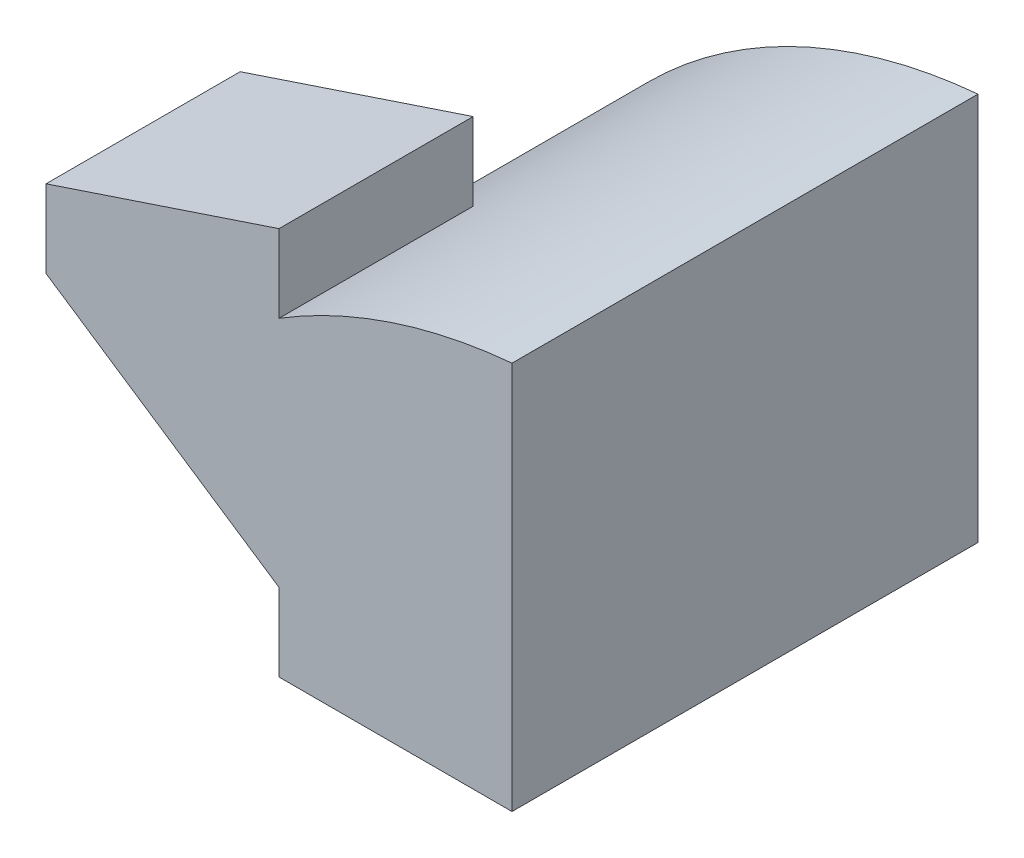
SolidWorks part; units mm, degrees
ref_plane "Front" through (0, 0, 0) normal (0, 0, 1) x (1, 0, 0)
ref_plane "Top" through (0, 0, 0) normal (0, 1, 0) x (1, 0, 0)
ref_plane "Right" through (0, 0, 0) normal (1, 0, 0) x (0, 0, -1)
sketch "Sketch1" plane through (0, 0, 0) normal (0, 1, 0) x (1, 0, 0)
  line L1 (-3, -3) -> (3, -3)
  line L2 (-3, -3) -> (-3, 3)
  line L3 (-3, 3) -> (3, 3)
  line L4 (3, -3) -> (3, 3)
  line L5 (-3, -3) -> (3, 3) construction
  line L6 (-3, 3) -> (3, -3) construction
  point P0 (0, 0)
  dimension "D1" = 6
  dimension "D2" = 6
extrude "Boss-Extrude1" add sketch "Sketch1" along normal blind 5
sketch "Sketch13" plane through (0, 0, -3) normal (0, 0, -1) x (-1, 0, 0)
  line L0 (3, 0) -> (-3, 0) construction
  line L1 (-3, 5) -> (-3, 0) construction
  line L6 (-3, 0) -> (3, 0)
  line L7 (-3, 5) -> (-3, 0)
  line L8 (3, 5) -> (-3, 5)
  line L9 (3, 0) -> (3, 5)
  line L10 (-3, 0) -> (3, 0)
  line L11 (-3, 5) -> (-3, 0)
  line L12 (3, 5) -> (-3, 5)
  line L13 (3, 0) -> (3, 5)
  arc A0 (-3, 5) -> (3, 0) centre (-3.6111, -1.8333) cw
  point P3 (0, 4)
  line M6 (3, 0) -> (3, 5)
  line M7 (3, 5) -> (-3, 5)
  dimension "D1" = 4
  dimension "D2" = 3
  dimension "D3" = 0
extrude "Cut-Extrude12" cut sketch "Sketch13" against normal blind 3.5 contours A0 M7 M6
sketch "Sketch14" plane through (0, 0, 0.5) normal (0, 0, -1) x (-1, 0, 0)
  line L0 (0, 4) -> (0, 5)
  line L2 (3, 5) -> (-3, 5)
  line L3 (3, 0) -> (3, 5)
  line L4 (3, 5) -> (-3, 5)
  line L5 (3, 0) -> (3, 5)
  arc A1 (3, 0) -> (-3, 5) centre (-3.6111, -1.8333) ccw
  arc A2 (3, 0) -> (-3, 5) centre (-3.6111, -1.8333) ccw
  line M4 (3, 5) -> (-3, 5)
  arc M5 (-3, 5) -> (3, 0) centre (-3.6111, -1.8333) cw
  dimension "D1" = 0
extrude "Cut-Extrude13" cut sketch "Sketch14" against normal blind 3.5 contours L0 M5 M4
sketch "Sketch15" plane through (0, 0, 3) normal (0, 0, 1) x (1, 0, 0)
  line L0 (0, 5) -> (-3, 4)
  line L1 (-3, 5) -> (-3, 0) construction
  line L2 (-3, 3) -> (0, 1)
  line L3 (0, 1) -> (0, 0)
  line L7 (3, 0) -> (3, 5)
  line L8 (0, 4) -> (0, 5)
  line L9 (0, 5) -> (-3, 5)
  line L10 (-3, 5) -> (-3, 0)
  line L11 (-3, 0) -> (3, 0)
  line L12 (3, 0) -> (3, 5)
  line L13 (0, 4) -> (0, 5)
  line L14 (0, 5) -> (-3, 5)
  line L15 (-3, 5) -> (-3, 0)
  line L16 (-3, 0) -> (3, 0)
  arc A1 (3, 5) -> (0, 4) centre (3.6111, -1.8333) ccw
  arc A2 (3, 5) -> (0, 4) centre (3.6111, -1.8333) ccw
  line M11 (0, 5) -> (-3, 5)
  line M12 (-3, 5) -> (-3, 0)
  line M13 (-3, 0) -> (3, 0)
  dimension "D2" = 1
  dimension "D3" = 1
  dimension "D4" = 1
  dimension "D1" = 0
extrude "Cut-Extrude14" cut sketch "Sketch15" against normal blind 3.5 contours L0 M11 M12 | L3 L2 M12 M13
